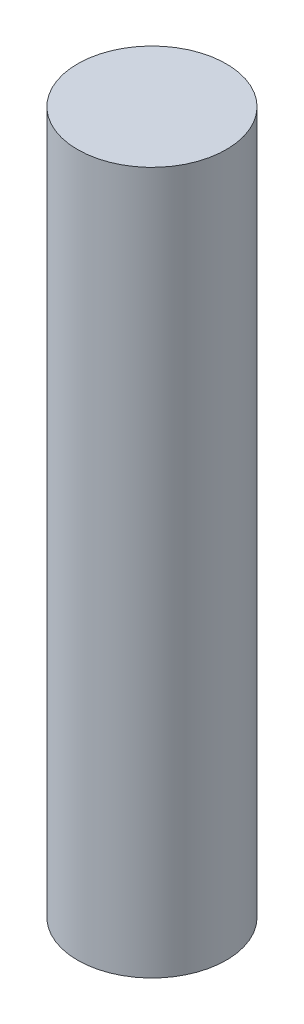
SolidWorks part; units mm, degrees
ref_plane "Front Plane" through (0, 0, 0) normal (0, 0, 1) x (1, 0, 0)
ref_plane "Top Plane" through (0, 0, 0) normal (0, 1, 0) x (1, 0, 0)
ref_plane "Right Plane" through (0, 0, 0) normal (1, 0, 0) x (0, 0, -1)
sketch "Sketch1" plane through (0, 0, 0) normal (0, 1, 0) x (1, 0, 0)
  circle A0 centre (0, 0) radius 914.4
  dimension "D1" = 1828.8
extrude "Boss-Extrude1" add sketch "Sketch1" along normal blind 8636
